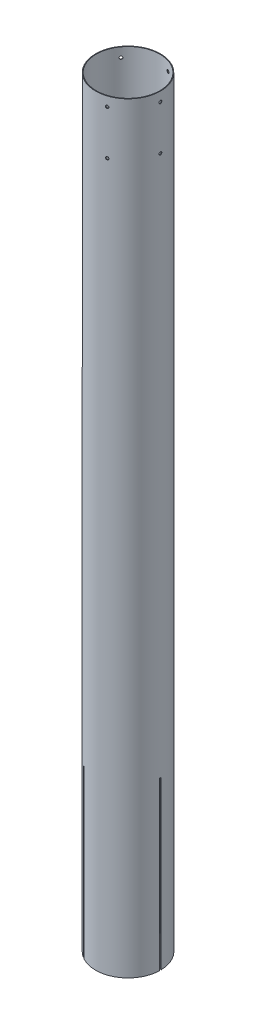
SolidWorks part; units mm, degrees
ref_plane "Front Plane" through (0, 0, 0) normal (0, 0, 1) x (1, 0, 0)
ref_plane "Top Plane" through (0, 0, 0) normal (0, 1, 0) x (1, 0, 0)
ref_plane "Right Plane" through (0, 0, 0) normal (1, 0, 0) x (0, 0, -1)
sketch "Sketch1" plane through (0, 0, 0) normal (0, 1, 0) x (1, 0, 0)
  circle A0 centre (0, 0) radius 58.3
  dimension "D1" = 116.6
extrude "Boss-Extrude1" add sketch "Sketch1" along normal blind 1370.17
sketch "Sketch2" plane through (0, 0, 0) normal (0, 1, 0) x (1, 0, 0)
  circle A0 centre (0, 0) radius 57.15
  dimension "D1" = 114.3
extrude "Cut-Extrude1" cut sketch "Sketch2" along normal blind 1370.17
ref_plane "Plane1" through (58.3, 0, 0) normal (1, 0, 0) x (0, 0, -1)
sketch "Sketch3" plane through (58.3, 0, 0) normal (1, 0, 0) x (0, 0, -1)
  line L0 (0, 64.13) -> (0, -64.13) construction
  line L1 (-1.5, 300) -> (1.5, 300)
  line L2 (-1.5, 300) -> (-1.5, 0)
  line L3 (-1.5, 0) -> (1.5, 0)
  line L4 (1.5, 300) -> (1.5, 0)
  line L5 (-1.5, 300) -> (1.5, 0) construction
  line L6 (-1.5, 0) -> (1.5, 300) construction
  line L7 (64.13, 0) -> (-64.13, 0) construction
  point P0 (0, 150)
  dimension "D1" = 3
  dimension "D2" = 300
extrude "Cut-Extrude2" cut sketch "Sketch3" against normal blind 10
pattern_circular "CirPattern1" count 3 over 360 about axis through (0, 0, 0) along (0, 1, 0) of "Cut-Extrude2"
hole_wizard "#6 (0.204) Diameter Hole1" positions "Sketch9" profile "Sketch10" hole size "#6" standard "ANSI Inch"
sketch "Sketch9" plane through (58.3, 0, 0) normal (1, 0, 0) x (0, 0, -1)
  line L0 (0, 64.13) -> (0, -64.13) construction
  line L1 (0, 1353.1774) -> (0, 1370.17)
  line L2 (57.15, 1370.17) -> (-57.15, 1370.17) construction
  line L4 (0, 1353.1774) -> (0, 1273.1674)
  point P0 (0, 1353.1774)
  point P4 (0, 1273.1674)
  dimension "D1" = 16.9926
  dimension "D2" = 80.01
sketch "Sketch10" plane through (58.3, 1353.1774, 0) normal (0, 1, 0) x (0, 0, -1)
  line L0 (0, 0) -> (0, 116.6)
  line L1 (0, 116.6) -> (2.5908, 116.6)
  line L2 (2.5908, 116.6) -> (2.5908, 0)
  line L5 (2.5908, 0) -> (0, 0)
  line L11 (0, -6.35) -> (0, 107.95) construction
  dimension "Thru Hole Dia." = 5.1816
  dimension "Thru Hole Depth" = 116.6
sketch "Sketch12" plane through (0, 0, 0) normal (1, 0, 0) x (0, 0, -1)
  line L0 (0, 1229.5145) -> (0, 1161.4597)
  line L1 (0, 64.13) -> (0, -64.13) construction
pattern_circular "CirPattern2" count 5 over 360 of "#6 (0.204) Diameter Hole1"
